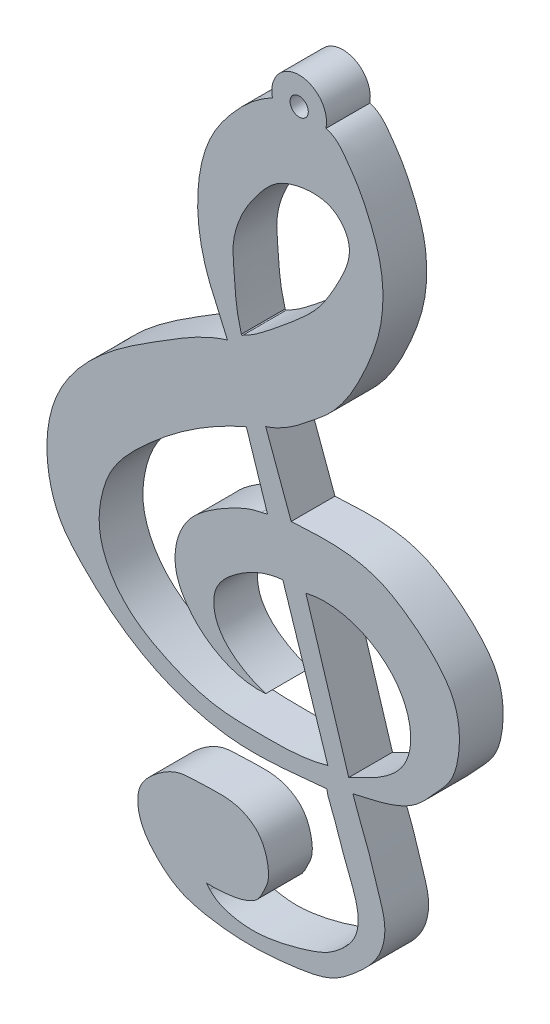
SolidWorks part; units mm, degrees
ref_plane "Alzado" through (0, 0, 0) normal (0, 0, 1) x (1, 0, 0)
ref_plane "Planta" through (0, 0, 0) normal (0, 1, 0) x (1, 0, 0)
ref_plane "Vista lateral" through (0, 0, 0) normal (1, 0, 0) x (0, 0, -1)
sketch "Croquis1" plane through (0, 0, 0) normal (0, 0, 1) x (1, 0, 0)
  line L0 (-75.7484, -1.1336) -> (-73.2794, -8.717)
  line L5 (-74.4845, -1.1336) -> (-72.133, -8.717)
  line L7 (-76.6889, 5.6788) -> (-75.2887, 1.8672)
  line L8 (-77.7478, 5.1343) -> (-76.5838, 1.5591)
  arc A0 (-73.3828, 21.4852) -> (-76.3154, 21.4647) centre (-74.8513, 21.791) ccw
  circle A1 centre (-74.8513, 21.791) radius 0.5
  spline S0 degree 3 poles (-76.6889, -7.0122) (-77.7403, -6.6698) (-79.4933, -5.6873) (-79.6097, -3.2535) (-78.048, -1.8232) (-76.6909, -1.2167) (-75.7484, -1.1336) knots 0 0 0 0 0.383378 0.517271 0.709393 1 1 1 1
  spline S1 degree 3 poles (-74.4845, -1.1336) (-73.2834, -0.8503) (-71.4401, -1.186) (-69.6335, -2.6102) (-68.8354, -3.973) (-68.6446, -5.3768) (-69.0978, -6.878) (-70.4438, -7.9553) (-71.5945, -8.4367) (-72.133, -8.717) knots 0 0 0 0 0.278394 0.399127 0.515243 0.629976 0.711946 0.862107 1 1 1 1
  spline S2 degree 1 poles (-76.5838, 1.5591) (-76.9241, 1.4824) knots 0 0 1 1
  spline S3 degree 3 poles (-71.9061, -9.3746) (-71.6128, -10.2668) (-71.0368, -11.5531) (-70.5283, -13.3595) (-70.0007, -14.7942) (-70.3895, -16.5351) (-71.6151, -17.6996) (-73.0608, -18.8844) (-74.9552, -19.1998) (-77.2419, -19.4389) (-79.4431, -19.3178) (-81.4338, -18.831) (-82.4647, -17.9803) (-83.141, -17.2525) (-83.594, -16.4808) (-83.753, -15.6175) (-83.6086, -14.786) (-83.1948, -14.2635) (-82.7029, -13.8236) (-82.1793, -13.4417) (-81.4321, -13.0929) (-80.5171, -13.0643) (-79.4925, -13.0164) (-78.2791, -13.0205) (-77.0162, -13.6664) (-76.5552, -14.8621) (-76.4886, -15.8389) (-76.8153, -16.4589) (-77.0651, -17.0202) (-77.7429, -17.4017) (-78.7067, -17.6036) (-79.4827, -17.645) (-79.9251, -17.6291) knots 0 0 0 0 0.074805 0.111322 0.14963 0.194578 0.242981 0.281555 0.341328 0.390462 0.465399 0.516027 0.549473 0.569858 0.595053 0.619443 0.638198 0.660324 0.670723 0.690791 0.711746 0.735034 0.762614 0.79371 0.830998 0.866508 0.890979 0.905817 0.921676 0.93857 0.964779 1 1 1 1
  spline S4 degree 3 poles (-73.3261, -9.8533) (-74.9797, -9.9958) (-78.4523, -10.4954) (-83.3882, -8.9145) (-86.2754, -6.4951) (-87.9572, -4.5644) (-88.5703, -2.9966) (-88.7758, -1.0138) (-88.306, 1.7296) (-85.9495, 4.6766) (-82.4258, 6.8697) (-80.045, 8.3597) (-78.784, 8.7351) knots 0 0 0 0 0.144811 0.299823 0.432277 0.467633 0.520862 0.574899 0.639454 0.757272 0.887089 1 1 1 1
  spline S5 degree 3 poles (-76.6889, -7.0122) (-77.78, -7.1011) (-79.3542, -6.6115) (-80.9083, -5.1916) (-81.725, -3.7942) (-81.6647, -2.1508) (-80.9788, -0.8071) (-80.0413, -0.0147) (-79.2351, 0.5035) (-78.2614, 1.0513) (-77.5003, 1.381) (-76.9241, 1.4824) knots 0 0 0 0 0.229659 0.335098 0.446803 0.564327 0.67037 0.760787 0.823624 0.875763 1 1 1 1
  spline S6 degree 1 poles (-79.7458, -17.8518) (-79.9251, -17.6291) knots 0 0 1 1
  spline S8 degree 2 poles (-77.928, 9.3959) (-77.977, 9.3166) (-78.0222, 9.3959) knots 0 0 0 1 1 1
  spline S9 degree 1 poles (-78.8313, 8.8264) (-78.784, 8.7351) knots 0 0 1 1
  spline S10 degree 3 poles (-79.7458, -17.8518) (-79.3777, -18.2505) (-78.5989, -18.5102) (-77.4455, -18.6415) (-76.3348, -18.5475) (-75.1932, -18.2915) (-74.1574, -17.9828) (-73.3286, -17.6559) (-72.6748, -17.1966) (-72.1369, -16.6847) (-71.7251, -16.0782) (-71.5579, -15.2507) (-71.7293, -14.277) (-72.076, -13.4116) (-72.3775, -12.6602) (-72.5466, -12.0926) (-72.7482, -11.5883) (-72.8958, -11.1126) (-73.0653, -10.7008) (-73.2352, -10.2833) (-73.3173, -10.0266) (-73.3261, -9.8533) knots 0 0 0 0 0.100297 0.155435 0.22444 0.315021 0.381826 0.433978 0.486801 0.535484 0.577524 0.62671 0.694738 0.765896 0.807411 0.851577 0.880545 0.912597 0.948032 0.966789 1 1 1 1
  spline S11 degree 3 poles (-75.2887, 1.8672) (-74.4684, 1.9083) (-72.8726, 2.0155) (-70.6315, 1.6751) (-68.8104, 0.5656) (-67.3898, -0.6255) (-66.1537, -2.2567) (-65.9617, -4.235) (-66.3654, -6.0094) (-67.4592, -7.1482) (-68.2705, -8.1232) (-69.8547, -8.9598) (-71.0542, -9.1663) (-71.9061, -9.3746) knots 0 0 0 0 0.117623 0.23029 0.317393 0.419587 0.496457 0.603597 0.693697 0.746524 0.827441 0.873617 1 1 1 1
  spline S12 degree 3 poles (-78.0222, 9.3959) (-78.1122, 9.7431) (-78.2846, 10.4078) (-78.3642, 11.4094) (-78.4343, 12.3402) (-78.5129, 13.223) (-78.4001, 13.9972) (-78.1459, 14.7747) (-77.7823, 15.5588) (-77.2393, 16.3136) (-76.6981, 17.0181) (-75.9484, 17.6798) (-74.9224, 18.0194) (-73.9231, 18.1085) (-72.8265, 17.872) (-72.0628, 16.966) (-72.1028, 15.784) (-72.5205, 14.8564) (-73.1079, 13.753) (-73.7785, 12.7066) (-74.6781, 11.8512) (-75.6185, 11.0489) (-76.6284, 10.2348) (-77.4242, 9.6403) (-77.8677, 9.4252) (-77.928, 9.3959) knots 0 0 0 0 0.046234 0.0885 0.129376 0.166981 0.202561 0.229436 0.272508 0.313509 0.349202 0.387286 0.440603 0.485479 0.515571 0.583511 0.614582 0.664466 0.712997 0.776704 0.823501 0.872685 0.936377 0.99134 1 1 1 1
  spline S13 degree 3 poles (-73.2794, -8.717) (-74.544, -9.0993) (-76.5979, -9.0858) (-79.6446, -9.0681) (-81.9323, -8.2263) (-83.9574, -7.1106) (-85.2735, -5.6214) (-85.9149, -3.853) (-85.7599, -2.2014) (-85.2826, -0.736) (-84.3926, 0.4562) (-83.2708, 1.5397) (-81.2075, 3.3144) (-79.2824, 4.4725) (-77.7478, 5.1343) knots 0 0 0 0 0.140602 0.223478 0.328348 0.401005 0.472812 0.539193 0.598886 0.649529 0.704842 0.75815 0.818924 1 1 1 1
  spline S15 degree 3 poles (-78.784, 8.7351) (-79.1488, 9.6345) (-80.225, 11.6466) (-80.6129, 14.9502) (-79.9079, 17.8263) (-78.3797, 19.9213) (-77.2015, 21.0205) (-76.3154, 21.4647) knots 0 0 0 0 0.201336 0.468683 0.6683 0.798365 1 1 1 1
  spline S16 degree 3 poles (-73.3828, 21.4852) (-72.8163, 21.3526) (-72.29, 20.6179) (-71.5634, 19.5726) (-70.9554, 18.3033) (-70.1803, 16.2797) (-70.2101, 13.6244) (-71.1184, 11.2741) (-72.0347, 9.4313) (-73.061, 8.0932) (-74.1765, 7.2115) (-75.2453, 6.3414) (-76.1053, 5.8549) (-76.6889, 5.6788) knots 0 0 0 0 0.08272 0.135601 0.197596 0.299487 0.468924 0.591754 0.687029 0.786865 0.848882 0.906336 1 1 1 1
extrude "Saliente-Extruir1" add sketch "Croquis1" along normal blind 2.4 contours S16 A0 S15 S4 S10 S6 S3 S11 L7 A1 L5 S1 S8 S12 L0 S13 L8 S2 S5 S0
